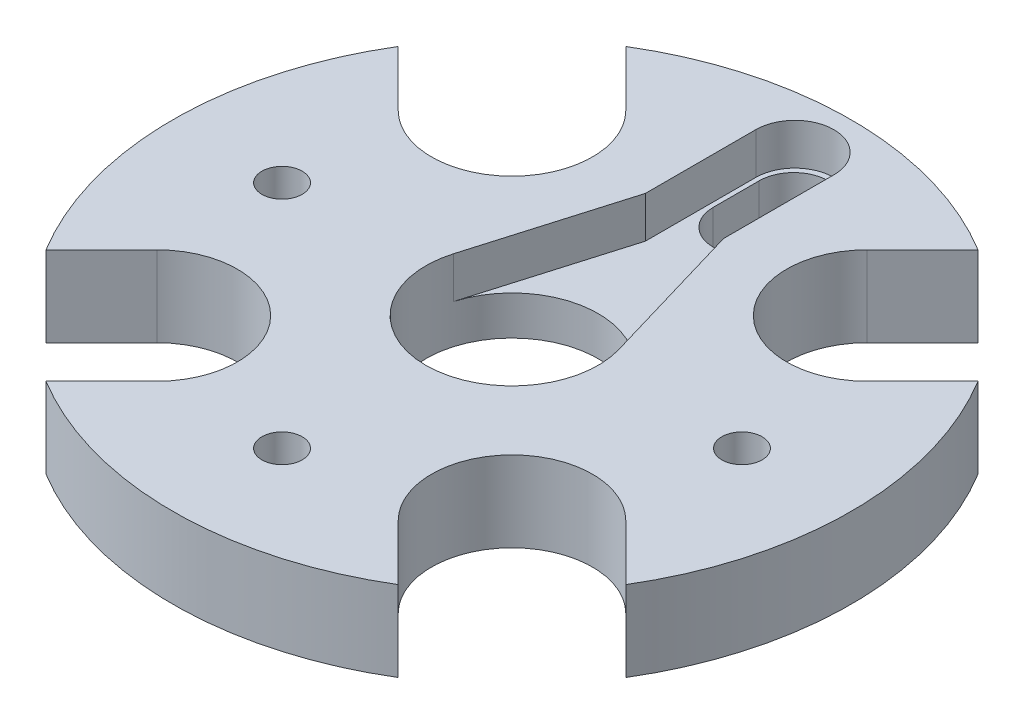
SolidWorks part; units mm, degrees
ref_plane "Front Plane" through (0, 0, 0) normal (0, 0, 1) x (1, 0, 0)
ref_plane "Top Plane" through (0, 0, 0) normal (0, 1, 0) x (1, 0, 0)
ref_plane "Right Plane" through (0, 0, 0) normal (1, 0, 0) x (0, 0, -1)
sketch "Sketch3" plane through (0, 0, 0) normal (0, 1, 0) x (1, 0, 0)
  circle A0 centre (0, 0) radius 29.5
  dimension "D1" = 59
extrude "Boss-Extrude4" add sketch "Sketch3" along normal blind 7
sketch "Sketch4" plane through (0, 7, 0) normal (0, 1, 0) x (1, 0, 0)
  line L0 (0, -7.5) -> (0, 28) construction
  line L1 (-3.4, 24.6) -> (-3.4, 15)
  line L2 (3.4, 24.6) -> (3.4, 15)
  line L3 (-3.4, 15) -> (-7.1943, 2.1193)
  line L4 (3.4, 15) -> (7.1943, 2.1193)
  arc A0 (-7.1943, 2.1193) -> (7.1943, 2.1193) centre (0, 0) ccw
  arc A1 (3.4, 24.6) -> (-3.4, 24.6) centre (0, 24.6) ccw
  dimension "D1" = 15
  dimension "D2" = 6.8
  dimension "D3" = 35.5
  dimension "D4" = 13
extrude "Cut-Extrude1" cut sketch "Sketch4" against normal blind 3.6
sketch "Sketch5" plane through (0, 7, 0) normal (0, 1, 0) x (1, 0, 0)
  line L0 (0, 24.5) -> (0, 20.5) construction
  line L1 (3, 24.5) -> (3, 20.5)
  line L2 (-3, 24.5) -> (-3, 20.5)
  line L3 (0, 27.5) -> (0, 28) construction
  line L4 (0, 27.5) -> (0, 17.5) construction
  circle A0 centre (0, 0) radius 7.5
  arc A1 (3, 24.5) -> (-3, 24.5) centre (0, 24.5) ccw
  arc A2 (-3, 20.5) -> (3, 20.5) centre (0, 20.5) ccw
  arc A4 (3.4, 24.6) -> (-3.4, 24.6) centre (0, 24.6) ccw construction
  point P7 (0, 22.5)
  dimension "D2" = 10
  dimension "D1" = 0.5
  dimension "D3" = 6
  dimension "D4" = 15
extrude "Cut-Extrude2" cut sketch "Sketch5" against normal blind 11.8
sketch "Sketch6" plane through (0, 7, 0) normal (0, 1, 0) x (1, 0, 0)
  line L0 (0, 0) -> (10.4935, 10.4935) construction
  line L1 (0, 0) -> (42.3991, 0) construction
  line L2 (15.4432, 15.4432) -> (20.393, 10.4935) construction
  line L3 (20.393, 10.4935) -> (32.6107, 22.7112)
  line L4 (15.4432, 15.4432) -> (10.4935, 20.393) construction
  line L5 (10.4935, 20.393) -> (22.7112, 32.6107)
  line L6 (32.6107, 22.7112) -> (22.7112, 32.6107)
  line L7 (10.4935, -20.393) -> (22.7112, -32.6107)
  line L8 (20.393, -10.4935) -> (32.6107, -22.7112)
  line L9 (22.7112, -32.6107) -> (32.6107, -22.7112)
  line L10 (-20.393, -10.4935) -> (-32.6107, -22.7112)
  line L11 (-10.4935, -20.393) -> (-22.7112, -32.6107)
  line L12 (-32.6107, -22.7112) -> (-22.7112, -32.6107)
  line L13 (-10.4935, 20.393) -> (-22.7112, 32.6107)
  line L14 (-20.393, 10.4935) -> (-32.6107, 22.7112)
  line L15 (-22.7112, 32.6107) -> (-32.6107, 22.7112)
  arc A0 (10.4935, 20.393) -> (20.393, 10.4935) centre (15.4432, 15.4432) ccw
  arc A1 (20.393, -10.4935) -> (10.4935, -20.393) centre (15.4432, -15.4432) ccw
  arc A2 (-10.4935, -20.393) -> (-20.393, -10.4935) centre (-15.4432, -15.4432) ccw
  arc A3 (-20.393, 10.4935) -> (-10.4935, 20.393) centre (-15.4432, 15.4432) ccw
  point P14 (0, 0)
  point P27 (0, 0)
  dimension "D3" = 14
  dimension "D1" = 14.84
extrude "Cut-Extrude3" cut sketch "Sketch6" against normal blind 15.8
extrude "Cut-Extrude4" cut sketch "Sketch7" against normal blind 20
sketch "Sketch7" plane through (116.3307, 17, -202.2831) normal (0, 1, 0) x (0.7071, 0, 0.7071)
  line L0 (60.7775, -225.294) -> (84.0315, -202.04) construction
  line L1 (60.7775, -225.294) -> (117.7906, -225.294) construction
  circle A0 centre (74.9197, -211.1519) radius 1.75
  circle A1 centre (74.9197, -239.4362) radius 1.75
  circle A2 centre (46.6354, -239.4362) radius 1.75
  point P15 (60.7775, -225.294)
sketch "Sketch8" plane through (0, 0, 0) normal (0, -1, 0) x (1, 0, 0)
  circle A0 centre (0, 20) radius 3.75
  circle A1 centre (20, 0) radius 3.75
  circle A2 centre (-20, 0) radius 3.75
  dimension "D1" = 7.5
extrude "Cut-Extrude5" cut sketch "Sketch8" against normal blind 2.4
